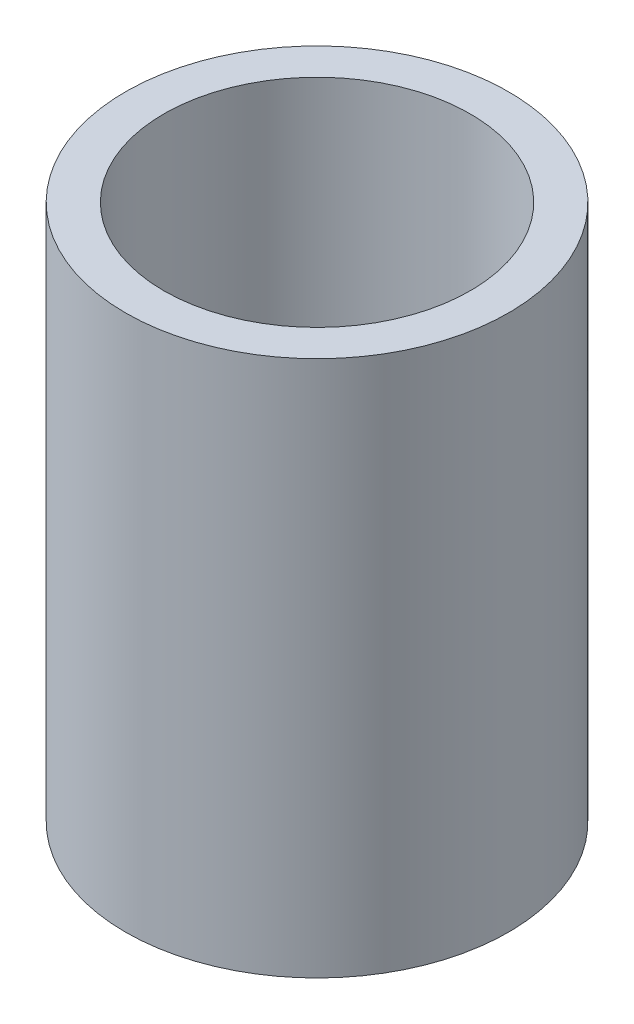
SolidWorks part; units mm, degrees
ref_plane "Front Plane" through (0, 0, 0) normal (0, 0, 1) x (1, 0, 0)
ref_plane "Top Plane" through (0, 0, 0) normal (0, 1, 0) x (1, 0, 0)
ref_plane "Right Plane" through (0, 0, 0) normal (1, 0, 0) x (0, 0, -1)
sketch "Sketch1" plane through (0, 0, 0) normal (0, 1, 0) x (1, 0, 0)
  circle A0 centre (0, 0) radius 5
  circle A1 centre (0, 0) radius 4
extrude "Boss-Extrude1" add sketch "Sketch1" along normal blind 14
